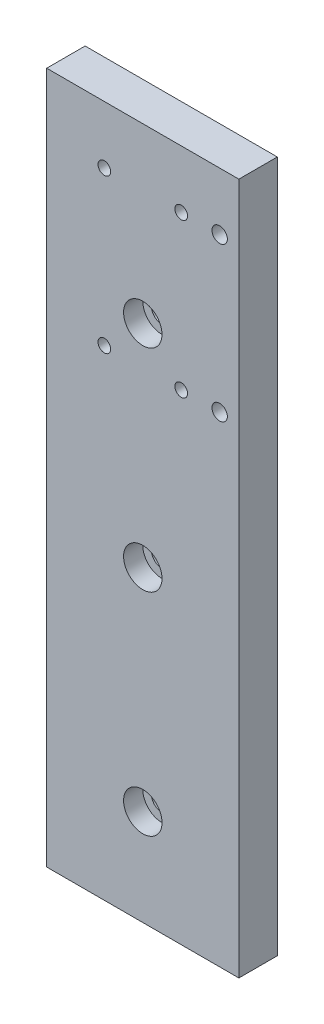
SolidWorks part; units mm, degrees
ref_plane "Front Plane" through (0, 0, 0) normal (0, 0, 1) x (1, 0, 0)
ref_plane "Top Plane" through (0, 0, 0) normal (0, 1, 0) x (1, 0, 0)
ref_plane "Right Plane" through (0, 0, 0) normal (1, 0, 0) x (0, 0, -1)
sketch "Sketch1" plane through (0, 0, 0) normal (0, 0, 1) x (1, 0, 0)
  line L1 (-35.9813, 35.8061) -> (14.0187, 35.8061)
  line L2 (-35.9813, 35.8061) -> (-35.9813, -144.1939)
  line L3 (-35.9813, -144.1939) -> (14.0187, -144.1939)
  line L4 (14.0187, 35.8061) -> (14.0187, -144.1939)
  line L5 (-35.9813, 35.8061) -> (14.0187, -144.1939) construction
  line L6 (-35.9813, -144.1939) -> (14.0187, 35.8061) construction
  circle A0 centre (-10.9813, -119.1939) radius 2.75
  circle A1 centre (-10.9813, -64.1939) radius 2.75
  circle A2 centre (-10.9813, -9.1939) radius 2.75
  circle A3 centre (9.0187, 20.8061) radius 2
  circle A4 centre (9.0187, -19.1939) radius 2
  point P0 (-10.9813, -54.1939)
  point P15 (0, 0)
  dimension "D3" = 25
  dimension "D4" = 5.5
  dimension "D6" = 135
  dimension "D7" = 4
  dimension "D8" = 5
  dimension "D9" = 15
  dimension "D10" = 125
  dimension "D1" = 50
  dimension "D2" = 180
  dimension "D5" = 80
extrude "Boss-Extrude1" add sketch "Sketch1" along normal blind 10
sketch "Sketch2" plane through (0, 0, 10) normal (0, 0, 1) x (1, 0, 0)
  circle A0 centre (-10.9813, -9.1939) radius 5
  circle A1 centre (-10.9813, -64.1939) radius 5
  circle A2 centre (-10.9813, -119.1939) radius 5
  dimension "D1" = 10
extrude "Cut-Extrude1" cut sketch "Sketch2" against normal blind 5
hole_wizard "M4 Tapped Hole1" positions "Sketch3" profile "Sketch4" tap size "M4" standard "ISO" end condition through all
sketch "Sketch3" plane through (0, 0, 10) normal (0, 0, 1) x (1, 0, 0)
  line L0 (-35.9813, 35.8061) -> (-35.9813, -144.1939) construction
  line L1 (14.0187, 35.8061) -> (-35.9813, 35.8061) construction
  point P0 (-0.9813, -19.1939)
  point P2 (-20.9813, -19.1939)
  point P4 (-20.9813, 20.8061)
  point P6 (-0.9813, 20.8061)
  point P8 (0, 0)
  point P9 (0, 0)
  dimension "D1" = 15
  dimension "D2" = 20
  dimension "D3" = 40
  dimension "D4" = 15
sketch "Sketch4" plane through (-0.9813, -19.1939, 10) normal (1, 0, 0) x (0, -1, 0)
  line L0 (0, 0) -> (0, 10)
  line L1 (0, 10) -> (1.65, 10)
  line L2 (1.65, 10) -> (1.65, 0)
  line L5 (1.65, 0) -> (0, 0)
  line L11 (0, -6.35) -> (0, 107.95) construction
  dimension "Thru Tap Drill Dia." = 3.3
  dimension "Thru Tap Drill Depth" = 10
cosmetic thread "Hole Thread1" parameters "D2"=4
cosmetic thread "Hole Thread2" parameters "D2"=4
cosmetic thread "Hole Thread3" parameters "D2"=4
cosmetic thread "Hole Thread4" parameters "D2"=4
hole_wizard "M4 Tapped Hole2" positions "Sketch5" profile "Sketch6" tap size "M4" standard "ISO"
sketch "Sketch5" plane through (0, -144.1939, 0) normal (0, -1, 0) x (-1, 0, 0)
  line L0 (35.9813, -10) -> (35.9813, 0) construction
  line L1 (35.9813, 0) -> (-14.0187, 0) construction
  point P0 (29.9813, -5)
  point P2 (-8.0187, -5)
  dimension "D1" = 6
  dimension "D2" = 44
  dimension "D3" = 5
  dimension "D4" = 5
sketch "Sketch6" plane through (-29.9813, -144.1939, 5) normal (1, 0, 0) x (0, 0, -1)
  line L0 (0, 0) -> (0, 8.9914)
  line L1 (0, 8.9914) -> (1.65, 8)
  line L2 (1.65, 8) -> (1.65, 0)
  line L5 (1.65, 0) -> (0, 0)
  line L10 (0, 8.9914) -> (-1.65, 8) construction
  line L11 (0, -6.35) -> (0, 107.95) construction
  dimension "Tap Drill Dia." = 3.3
  dimension "Tap Drill Depth" = 8
  dimension "Drill Angle" = 118
cosmetic thread "Hole Thread5" parameters "D1"=8, "D2"=4
cosmetic thread "Hole Thread6" parameters "D1"=8, "D2"=4
